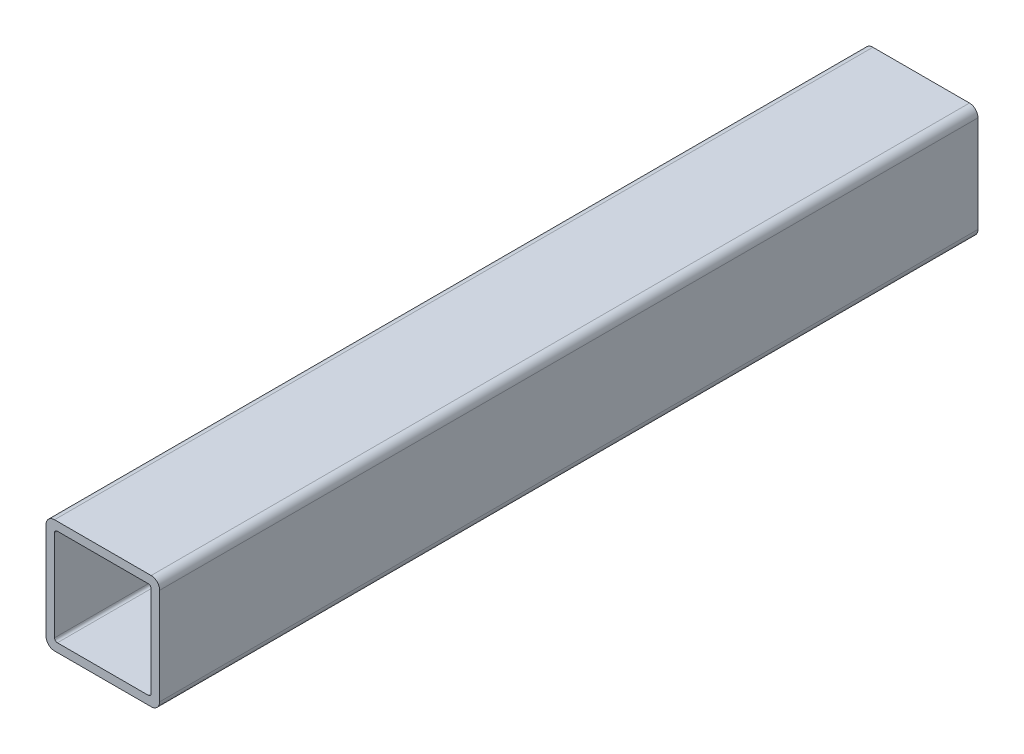
SolidWorks part; units mm, degrees
ref_plane "Front Plane" through (0, 0, 0) normal (0, 0, 1) x (1, 0, 0)
ref_plane "Top Plane" through (0, 0, 0) normal (0, 1, 0) x (1, 0, 0)
ref_plane "Right Plane" through (0, 0, 0) normal (1, 0, 0) x (0, 0, -1)
sketch "Sketch1" plane through (0, 0, 0) normal (0, 0, 1) x (1, 0, 0)
  line L1 (-26.9875, 31.75) -> (26.9875, 31.75)
  line L2 (-31.75, 26.9875) -> (-31.75, -26.9875)
  line L3 (-26.9875, -31.75) -> (26.9875, -31.75)
  line L4 (31.75, 26.9875) -> (31.75, -26.9875)
  line L5 (-31.75, 31.75) -> (31.75, -31.75) construction
  line L6 (-31.75, -31.75) -> (31.75, 31.75) construction
  line L7 (-25.4, 26.9875) -> (25.4, 26.9875)
  line L8 (-26.9875, 25.4) -> (-26.9875, -25.4)
  line L9 (-25.4, -26.9875) -> (25.4, -26.9875)
  line L10 (26.9875, 25.4) -> (26.9875, -25.4)
  line L11 (-26.9875, 26.9875) -> (26.9875, -26.9875) construction
  line L12 (-26.9875, -26.9875) -> (26.9875, 26.9875) construction
  arc A0 (-31.75, -26.9875) -> (-26.9875, -31.75) centre (-26.9875, -26.9875) ccw
  arc A1 (26.9875, -31.75) -> (31.75, -26.9875) centre (26.9875, -26.9875) ccw
  arc A2 (31.75, 26.9875) -> (26.9875, 31.75) centre (26.9875, 26.9875) ccw
  arc A3 (-26.9875, 31.75) -> (-31.75, 26.9875) centre (-26.9875, 26.9875) ccw
  arc A4 (-26.9875, -25.4) -> (-25.4, -26.9875) centre (-25.4, -25.4) ccw
  arc A5 (25.4, -26.9875) -> (26.9875, -25.4) centre (25.4, -25.4) ccw
  arc A6 (26.9875, 25.4) -> (25.4, 26.9875) centre (25.4, 25.4) ccw
  arc A7 (-25.4, 26.9875) -> (-26.9875, 25.4) centre (-25.4, 25.4) ccw
  point P0 (0, 0)
  point P6 (0, 0)
  dimension "D4" = 4.7625
  dimension "D5" = 1.5875
  dimension "D1" = 63.5
  dimension "D2" = 63.5
  dimension "D3" = 4.7625
  dimension "D6" = 4.7625
extrude "Boss-Extrude1" add sketch "Sketch1" along normal mid plane 457.2
sketch "Sketch2" plane through (0, -31.75, 0) normal (0, -1, 0) x (1, 0, 0)
  line L0 (0, 228.6) -> (0, -228.6) construction
  line L1 (-26.9875, 228.6) -> (26.9875, 228.6) construction
  line L2 (-26.9875, -228.6) -> (26.9875, -228.6) construction
  line L3 (-31.75, -174.625) -> (31.75, -174.625) construction
  line L4 (-31.75, 228.6) -> (-31.75, -228.6) construction
  line L5 (31.75, 228.6) -> (31.75, -228.6) construction
  line L6 (-31.75, 434.975) -> (31.75, 434.975) construction
  dimension "D1" = 53.975
  dimension "D2" = 609.6
sketch "Sketch3" plane through (-31.75, 0, 0) normal (-1, 0, 0) x (0, 0, 1)
  line L0 (-228.6, 0) -> (228.6, 0) construction
  line L1 (-228.6, 26.9875) -> (-228.6, -26.9875) construction
  line L2 (228.6, 26.9875) -> (228.6, -26.9875) construction
  line L3 (-203.2, 31.75) -> (-203.2, -31.75) construction
  line L4 (228.6, 31.75) -> (-228.6, 31.75) construction
  line L5 (228.6, -31.75) -> (-228.6, -31.75) construction
  line L6 (0, 31.75) -> (0, -31.75) construction
  line L7 (152.4, 31.75) -> (152.4, -31.75) construction
  line L8 (203.2, 31.75) -> (203.2, -31.75) construction
  dimension "D1" = 25.4
  dimension "D2" = 25.4
  dimension "D3" = 203.2
  dimension "D4" = 152.4
sketch "Sketch4" plane through (0, 0, -228.6) normal (0, 0, -1) x (-1, 0, 0)
  line L0 (0, 31.75) -> (0, -31.75) construction
  line L1 (-26.9875, 31.75) -> (26.9875, 31.75) construction
  line L2 (26.9875, -31.75) -> (-26.9875, -31.75) construction
  line L3 (31.75, 0) -> (-31.75, 0) construction
  line L4 (31.75, 26.9875) -> (31.75, -26.9875) construction
  line L5 (-31.75, -26.9875) -> (-31.75, 26.9875) construction
